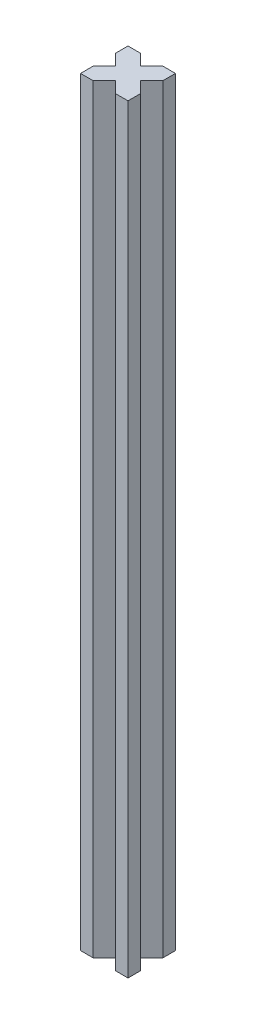
SolidWorks part; units mm, degrees
ref_plane "Front" through (0, 0, 0) normal (0, 0, 1) x (1, 0, 0)
ref_plane "Top" through (0, 0, 0) normal (0, 1, 0) x (1, 0, 0)
ref_plane "Right" through (0, 0, 0) normal (1, 0, 0) x (0, 0, -1)
sketch "Sketch1" plane through (0, 0, 0) normal (0, 1, 0) x (1, 0, 0)
  line L0 (0, 0) -> (4, 0)
  line L1 (0, 0) -> (0, 4)
  line L2 (15, 0) -> (15, 4)
  line L3 (0, 15) -> (4, 15)
  line L4 (4, 15) -> (7.5, 11.5)
  line L5 (7.5, 11.5) -> (11, 15)
  line L6 (15, 11) -> (11.5, 7.5)
  line L7 (11.5, 7.5) -> (15, 4)
  line L8 (11, 0) -> (7.5, 3.5)
  line L9 (7.5, 3.5) -> (4, 0)
  line L10 (0, 4) -> (3.5, 7.5)
  line L11 (3.5, 7.5) -> (0, 11)
  line L12 (-50, 0) -> (50, 0) construction
  line L13 (0, -50) -> (0, 50) construction
  line L14 (11, 15) -> (15, 15)
  line L15 (15, 11) -> (15, 15)
  line L16 (0, 11) -> (0, 15)
  line L17 (11, 0) -> (15, 0)
  point P16 (0, 0)
  point P19 (0, 0)
  point P21 (0, 0)
  point P23 (0, 0)
  point P25 (4.1166, 0)
  point P28 (10.3838, 15)
  point P29 (7.5, 12.0095)
  point P30 (5.233, 15)
  point P31 (0, 9.7062)
  point P34 (15, 11.7619)
  point P35 (10.1221, 0)
  dimension "D1" = 15
  dimension "D2" = 15
  dimension "D3" = 7
  dimension "D4" = 135
  dimension "D5" = 135
  dimension "D6" = 45
  dimension "D7" = 45
  dimension "D8" = 7
  dimension "D9" = 7
  dimension "D10" = 7
extrude "Boss-Extrude1" add sketch "Sketch1" along normal blind 240
